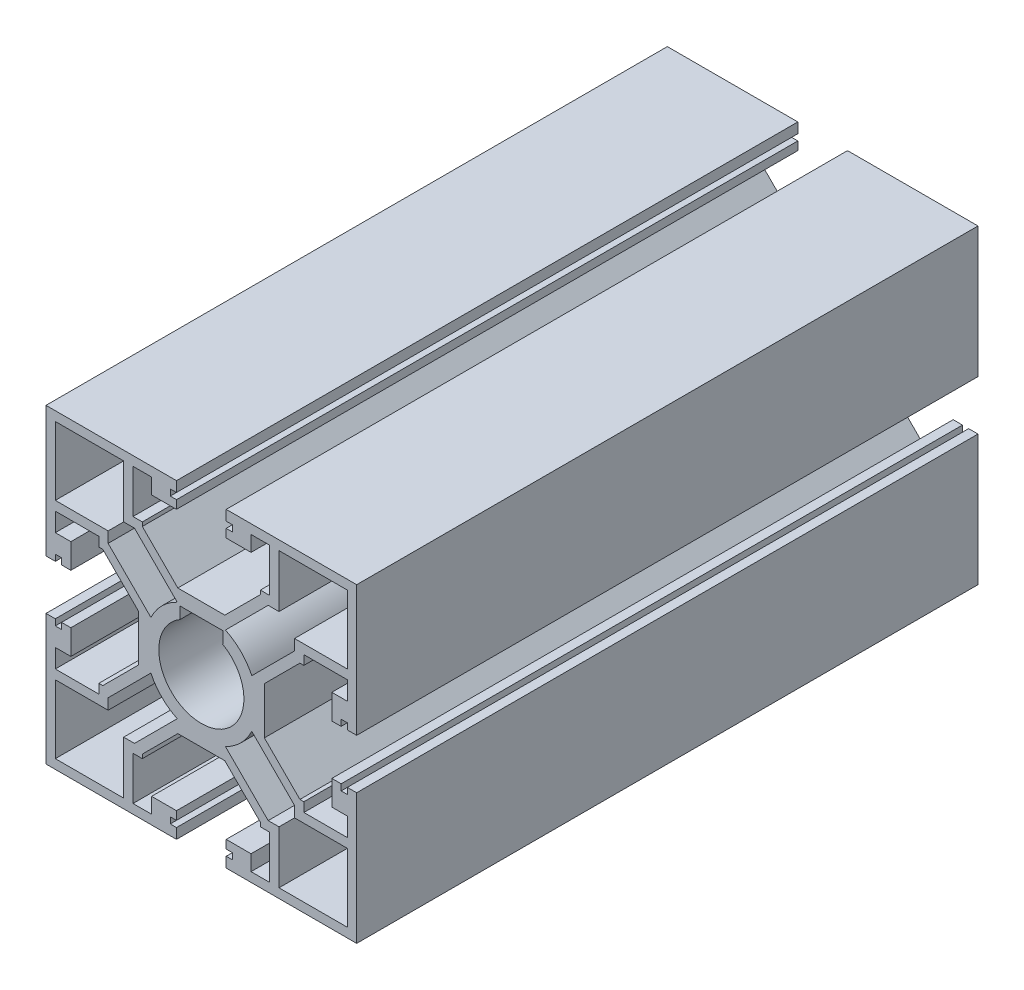
SolidWorks part; units mm, degrees
ref_plane "Front" through (0, 0, 0) normal (0, 0, 1) x (1, 0, 0)
ref_plane "Top" through (0, 0, 0) normal (0, 1, 0) x (1, 0, 0)
ref_plane "Right" through (0, 0, 0) normal (1, 0, 0) x (0, 0, -1)
sketch "A01-1" plane through (0, 0, 0) normal (0, 0, 1) x (1, 0, 0)
  line L0 (-23.5, 23.5) -> (-23.5, 12.5)
  line L1 (-23.5, 12.5) -> (-15, 12.5)
  line L2 (-12.5, 15) -> (-12.5, 23.5)
  line L3 (-12.5, 23.5) -> (-23.5, 23.5)
  line L6 (-23.5, 4) -> (-25, 4)
  line L7 (-4, 22.3498) -> (-4, 21)
  line L8 (10.146, -3.7821) -> (10.146, 3.7821)
  line L9 (10.146, 3.7821) -> (15.864, 9.5)
  line L10 (16.5, 11) -> (21, 11)
  line L11 (-11, 23.5) -> (-8, 23.5)
  line L12 (-8, 23.5) -> (-8, 21)
  line L13 (-11, 23.5) -> (-11, 21)
  line L14 (-23.5, 11) -> (-23.5, 8)
  line L15 (-4, 23.3498) -> (-5, 23.3498)
  line L16 (21, 8) -> (21, 4)
  line L17 (-4, 22.3498) -> (-5, 22.3498)
  line L18 (-5, 23.3498) -> (-5, 22.3498)
  line L19 (-23.5, 8) -> (-21, 8)
  line L20 (-23.5, 11) -> (-21, 11)
  line L21 (-8.1213, 3.8787) -> (-15, 10.7574)
  line L22 (21, 4) -> (22.5, 4)
  line L23 (-23.5, 4) -> (-23.5, 5)
  line L24 (-23.5, 5) -> (-22.5, 5)
  line L25 (-22.5, 4) -> (-22.5, 5)
  line L26 (-15, 10.7574) -> (-15, 12.5)
  line L27 (-3.8787, 8.1213) -> (-10.7574, 15)
  line L28 (-10.7574, 15) -> (-12.5, 15)
  line L29 (25, 4) -> (25, 25)
  line L30 (25, 25) -> (4, 25)
  line L31 (4, 25) -> (4, 23.3498)
  line L32 (4, 21) -> (8, 21)
  line L33 (11, 21) -> (11, 16.5)
  line L34 (9.5, 15.864) -> (3.7821, 10.146)
  line L35 (9.5, 16.5) -> (9.5, 15.864)
  line L36 (11, 16.5) -> (9.5, 16.5)
  line L37 (16.5, 9.5) -> (16.5, 11)
  line L38 (15.864, 9.5) -> (16.5, 9.5)
  line L39 (10.7574, 15) -> (12.5, 15)
  line L40 (3.8787, 8.1213) -> (10.7574, 15)
  line L41 (15, 10.7574) -> (15, 12.5)
  line L42 (22.5, 4) -> (22.5, 5)
  line L43 (23.5, 5) -> (22.5, 5)
  line L44 (23.5, 4) -> (23.5, 5)
  line L45 (8.1213, 3.8787) -> (15, 10.7574)
  line L46 (23.5, 11) -> (21, 11)
  line L47 (23.5, 8) -> (21, 8)
  line L48 (5, 23.3498) -> (5, 22.3498)
  line L49 (4, 22.3498) -> (5, 22.3498)
  line L50 (4, 23.3498) -> (5, 23.3498)
  line L51 (23.5, 11) -> (23.5, 8)
  line L52 (11, 23.5) -> (11, 21)
  line L53 (8, 23.5) -> (8, 21)
  line L54 (11, 23.5) -> (8, 23.5)
  line L55 (4, 22.3498) -> (4, 21)
  line L56 (23.5, 4) -> (25, 4)
  line L57 (12.5, 23.5) -> (23.5, 23.5)
  line L58 (12.5, 15) -> (12.5, 23.5)
  line L59 (23.5, 12.5) -> (15, 12.5)
  line L60 (23.5, 23.5) -> (23.5, 12.5)
  line L61 (-10.146, -3.7821) -> (-15.864, -9.5)
  line L62 (-16.5, -11) -> (-21, -11)
  line L63 (-21, -8) -> (-21, -4)
  line L64 (-21, -4) -> (-22.5, -4)
  line L65 (-25, -4) -> (-25, -25)
  line L66 (-25, -25) -> (-4, -25)
  line L67 (-4, -25) -> (-4, -23.3498)
  line L68 (-4, -21) -> (-8, -21)
  line L69 (-11, -21) -> (-11, -16.5)
  line L70 (-9.5, -15.864) -> (-3.7821, -10.146)
  line L71 (-3.7821, -10.146) -> (3.7821, -10.146)
  line L72 (-9.5, -16.5) -> (-9.5, -15.864)
  line L73 (-11, -16.5) -> (-9.5, -16.5)
  line L74 (-16.5, -9.5) -> (-16.5, -11)
  line L75 (-15.864, -9.5) -> (-16.5, -9.5)
  line L76 (23.5, -23.5) -> (23.5, -12.5)
  line L77 (23.5, -12.5) -> (15, -12.5)
  line L78 (-15.864, 9.5) -> (-16.5, 9.5)
  line L79 (-16.5, 9.5) -> (-16.5, 11)
  line L80 (-11, 16.5) -> (-9.5, 16.5)
  line L81 (-9.5, 16.5) -> (-9.5, 15.864)
  line L82 (12.5, -15) -> (12.5, -23.5)
  line L83 (12.5, -23.5) -> (23.5, -23.5)
  line L84 (23.5, -4) -> (25, -4)
  line L85 (4, -22.3498) -> (4, -21)
  line L86 (11, -23.5) -> (8, -23.5)
  line L87 (8, -23.5) -> (8, -21)
  line L88 (11, -23.5) -> (11, -21)
  line L89 (23.5, -11) -> (23.5, -8)
  line L90 (4, -23.3498) -> (5, -23.3498)
  line L91 (4, -22.3498) -> (5, -22.3498)
  line L92 (5, -23.3498) -> (5, -22.3498)
  line L93 (23.5, -8) -> (21, -8)
  line L94 (23.5, -11) -> (21, -11)
  line L95 (8.1213, -3.8787) -> (15, -10.7574)
  line L96 (23.5, -4) -> (23.5, -5)
  line L97 (23.5, -5) -> (22.5, -5)
  line L98 (22.5, -4) -> (22.5, -5)
  line L99 (15, -10.7574) -> (15, -12.5)
  line L100 (3.8787, -8.1213) -> (10.7574, -15)
  line L101 (10.7574, -15) -> (12.5, -15)
  line L102 (15.864, -9.5) -> (16.5, -9.5)
  line L103 (16.5, -9.5) -> (16.5, -11)
  line L104 (11, -16.5) -> (9.5, -16.5)
  line L105 (9.5, -16.5) -> (9.5, -15.864)
  line L106 (9.5, -15.864) -> (3.7821, -10.146)
  line L107 (11, -21) -> (11, -16.5)
  line L108 (4, -21) -> (8, -21)
  line L109 (4, -25) -> (4, -23.3498)
  line L110 (25, -25) -> (4, -25)
  line L111 (25, -4) -> (25, -25)
  line L112 (-10.7574, -15) -> (-12.5, -15)
  line L113 (-3.8787, -8.1213) -> (-10.7574, -15)
  line L114 (-3.7821, 10.146) -> (3.7821, 10.146)
  line L115 (-9.5, 15.864) -> (-3.7821, 10.146)
  line L116 (-11, 21) -> (-11, 16.5)
  line L117 (-4, 21) -> (-8, 21)
  line L118 (-4, 25) -> (-4, 23.3498)
  line L119 (-25, 25) -> (-4, 25)
  line L120 (-25, 4) -> (-25, 25)
  line L121 (-21, 4) -> (-22.5, 4)
  line L122 (-21, 8) -> (-21, 4)
  line L123 (-16.5, 11) -> (-21, 11)
  line L124 (-10.146, 3.7821) -> (-15.864, 9.5)
  line L125 (-10.146, -3.7821) -> (-10.146, 3.7821)
  line L126 (-15, -10.7574) -> (-15, -12.5)
  line L127 (-22.5, -4) -> (-22.5, -5)
  line L128 (-23.5, -5) -> (-22.5, -5)
  line L129 (-23.5, -4) -> (-23.5, -5)
  line L130 (21, -4) -> (22.5, -4)
  line L131 (-8.1213, -3.8787) -> (-15, -10.7574)
  line L132 (-23.5, -11) -> (-21, -11)
  line L133 (-23.5, -8) -> (-21, -8)
  line L134 (-5, -23.3498) -> (-5, -22.3498)
  line L135 (-4, -22.3498) -> (-5, -22.3498)
  line L136 (21, -8) -> (21, -4)
  line L137 (-4, -23.3498) -> (-5, -23.3498)
  line L138 (-23.5, -11) -> (-23.5, -8)
  line L139 (-11, -23.5) -> (-11, -21)
  line L140 (-8, -23.5) -> (-8, -21)
  line L141 (-11, -23.5) -> (-8, -23.5)
  line L142 (16.5, -11) -> (21, -11)
  line L143 (10.146, -3.7821) -> (15.864, -9.5)
  line L144 (-4, -22.3498) -> (-4, -21)
  line L145 (-23.5, -4) -> (-25, -4)
  line L146 (-12.5, -23.5) -> (-23.5, -23.5)
  line L147 (-12.5, -15) -> (-12.5, -23.5)
  line L148 (-23.5, -12.5) -> (-15, -12.5)
  line L149 (-23.5, -23.5) -> (-23.5, -12.5)
  arc A0 (8.1213, 3.8787) -> (3.8787, 8.1213) centre (0, 0) ccw
  circle A1 centre (0, 0) radius 6.85
  arc A2 (3.8787, -8.1213) -> (8.1213, -3.8787) centre (0, 0) ccw
  arc A3 (-8.1213, -3.8787) -> (-3.8787, -8.1213) centre (0, 0) ccw
  arc A4 (-3.8787, 8.1213) -> (-8.1213, 3.8787) centre (0, 0) ccw
  point P12 (-10.146, 0)
  point P157 (10.146, 0)
extrude "Extrude1" add sketch "A01-1" against normal blind 100
sketch "Sketch1" plane through (0, 0, 0) normal (0, 0, 1) x (1, 0, 0)
  line L1 (-3.4173, 5.9367) -> (3.4748, 5.9367)
  line L2 (-3.4173, 5.9367) -> (-3.4173, 7.8212)
  line L3 (-3.4173, 7.8212) -> (3.4748, 7.8212)
  line L4 (3.4748, 5.9367) -> (3.4748, 7.8212)
  circle A0 centre (0, 0) radius 6.85 construction
extrude "Cut-Extrude1" cut sketch "Sketch1" against normal through all
